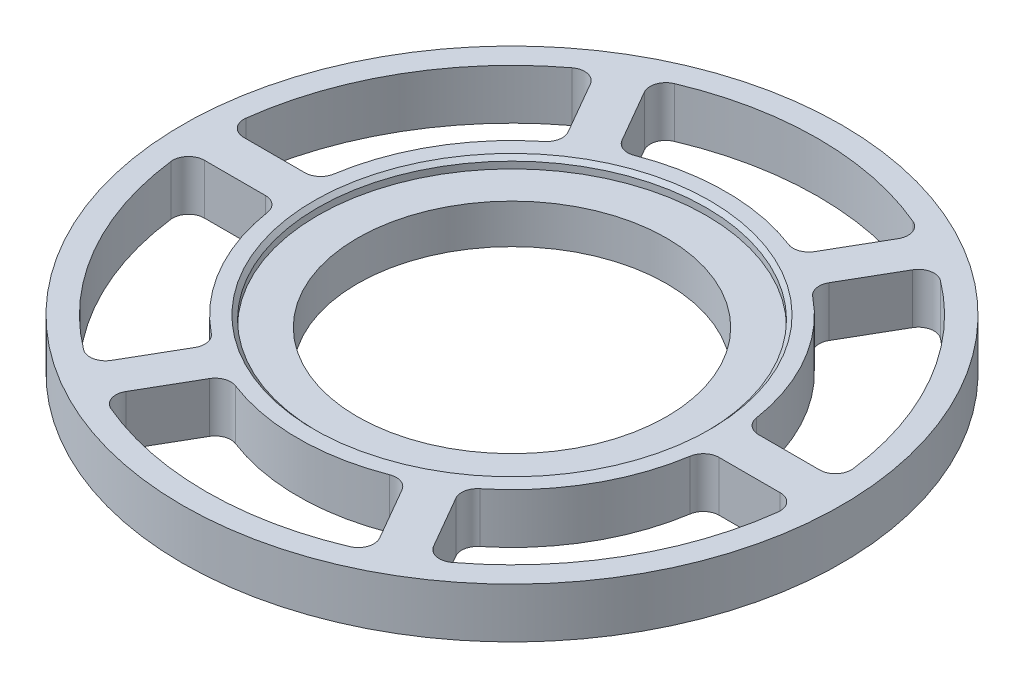
SolidWorks part; units mm, degrees
material "6061-T6 (SS)"
ref_plane "Front Plane" through (0, 0, 0) normal (0, 0, 1) x (1, 0, 0)
ref_plane "Top Plane" through (0, 0, 0) normal (0, 1, 0) x (1, 0, 0)
ref_plane "Right Plane" through (0, 0, 0) normal (1, 0, 0) x (0, 0, -1)
sketch "Sketch2" plane through (0, 0, 0) normal (1, 0, 0) x (0, 0, -1)
  line L0 (-39.2125, 0) -> (-82.55, 0)
  line L1 (-82.55, 0) -> (-82.55, 12.7)
  line L2 (-82.55, 12.7) -> (-49.2125, 12.7)
  line L3 (-49.2125, 12.7) -> (-49.2125, 10)
  line L4 (-49.2125, 10) -> (-39.2125, 10)
  line L5 (-39.2125, 10) -> (-39.2125, 0)
  dimension "D1" = 82.55
  dimension "D2" = 12.7
  dimension "D4" = 49.2125
  dimension "D5" = 10
  dimension "D3" = 10
ref_axis "Axis1" through (0, -0.9525, 0) along (0, 1, 0)
revolve "Revolve1" add sketch "Sketch2" angle 360 about axis through (0, -0.9525, 0) along (0, 1, 0)
hole_wizard "#6 (0.204) Diameter Hole1" positions "Sketch6" profile "Sketch7" hole size "#6" standard "ANSI Inch"
sketch "Sketch6" plane through (0, 12.7, 0) normal (0, 1, 0) x (1, 0, 0)
  line L0 (0, 0) -> (-69.8201, 120.932) construction
  line L2 (0, 0) -> (0, 109.0908) construction
  point P0 (-35, 60.6218)
  dimension "D1" = 30
  dimension "D2" = 70
sketch "Sketch7" plane through (-35, 12.7, -60.6218) normal (1, 0, 0) x (0, 0, 1)
  line L0 (0, 0) -> (0, 12.7)
  line L1 (0, 12.7) -> (2.5908, 12.7)
  line L2 (2.5908, 12.7) -> (2.5908, 0)
  line L5 (2.5908, 0) -> (0, 0)
  line L11 (0, -6.35) -> (0, 107.95) construction
  dimension "Thru Hole Dia." = 5.1816
  dimension "Thru Hole Depth" = 12.7
sketch "Sketch8" plane through (0, 12.7, 0) normal (0, 1, 0) x (1, 0, 0)
  line L0 (-34.3642, 69.5205) -> (-22.6606, 49.2493)
  line L1 (34.3642, 69.5205) -> (22.6606, 49.2493)
  line L2 (0, 0) -> (-35, 60.6218) construction
  line L4 (0, 0) -> (0, 93.9995) construction
  arc A0 (-22.6606, 49.2493) -> (22.6606, 49.2493) centre (0, 0) cw
  arc A1 (-34.3642, 69.5205) -> (34.3642, 69.5205) centre (0, 0) cw
  circle A2 centre (0, 0) radius 49.2125 construction
  circle A3 centre (0, 0) radius 82.55 construction
  point P6 (0, 0)
  dimension "D1" = 5
  dimension "D2" = 5
  dimension "D3" = 5
  dimension "D4" = 30
extrude "Cut-Extrude1" cut sketch "Sketch8" against normal through all
fillet "Fillet1" radius 4 4 edges at (34.3642, 6.35, -69.5205) (22.6606, 6.35, -49.2493) (-34.3642, 6.35, -69.5205) (-22.6606, 6.35, -49.2493)
pattern_circular "CirPattern4" count 6 over 360 about axis through (0, 0, 0) along (0, 1, 0) of "Cut-Extrude1", "Fillet1"
chamfer "Chamfer1" distance 1 angle 45 1 edges at (0, 12.7, -49.2125)
sketch "Sketch9" plane through (0, 0, 0) normal (0, -1, 0) x (1, 0, 0)
  circle A0 centre (0, 0) radius 82.55
  circle A1 centre (0, 0) radius 83.55
  circle A2 centre (0, 0) radius 82.55 construction
  dimension "D1" = 1
extrude "Boss-Extrude1" add sketch "Sketch9" against normal blind 12.7
equation "\"TubeDiameter\" = 6.500in"
equation "\"D1@Sketch2\"=\"TubeDiameter\"/2"
